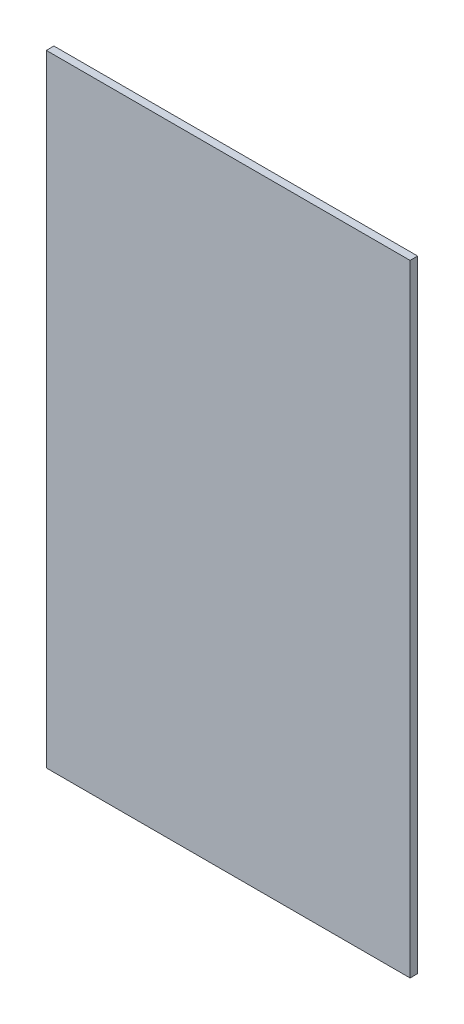
SolidWorks part; units mm, degrees
ref_plane "Front Plane" through (0, 0, 0) normal (0, 0, 1) x (1, 0, 0)
ref_plane "Top Plane" through (0, 0, 0) normal (0, 1, 0) x (1, 0, 0)
ref_plane "Right Plane" through (0, 0, 0) normal (1, 0, 0) x (0, 0, -1)
sketch "Sketch1" plane through (0, 0, 0) normal (0, 0, 1) x (1, 0, 0)
  line L1 (0, 0) -> (240, 0)
  line L2 (0, 0) -> (0, -410)
  line L3 (0, -410) -> (240, -410)
  line L4 (240, 0) -> (240, -410)
  dimension "D1" = 240
  dimension "D2" = 410
extrude "Boss-Extrude1" add sketch "Sketch1" along normal blind 5
sketch "Sketch2" [suppressed] plane through (0, -640, 0) normal (0, -1, 0) x (1, 0, 0)
  line L4 (0, 0) -> (470, 0)
  line L5 (470, 0) -> (470, 5)
  line L6 (470, 5) -> (0, 5)
  line L7 (0, 5) -> (0, 0)
  line L8 (0, 0) -> (470, 0)
  line L9 (470, 0) -> (470, 5)
  line L10 (470, 5) -> (0, 5)
  line L11 (0, 5) -> (0, 0)
  dimension "D1" = 0
extrude "Cut-Extrude1" [suppressed] cut sketch "Sketch2" against normal blind 220
